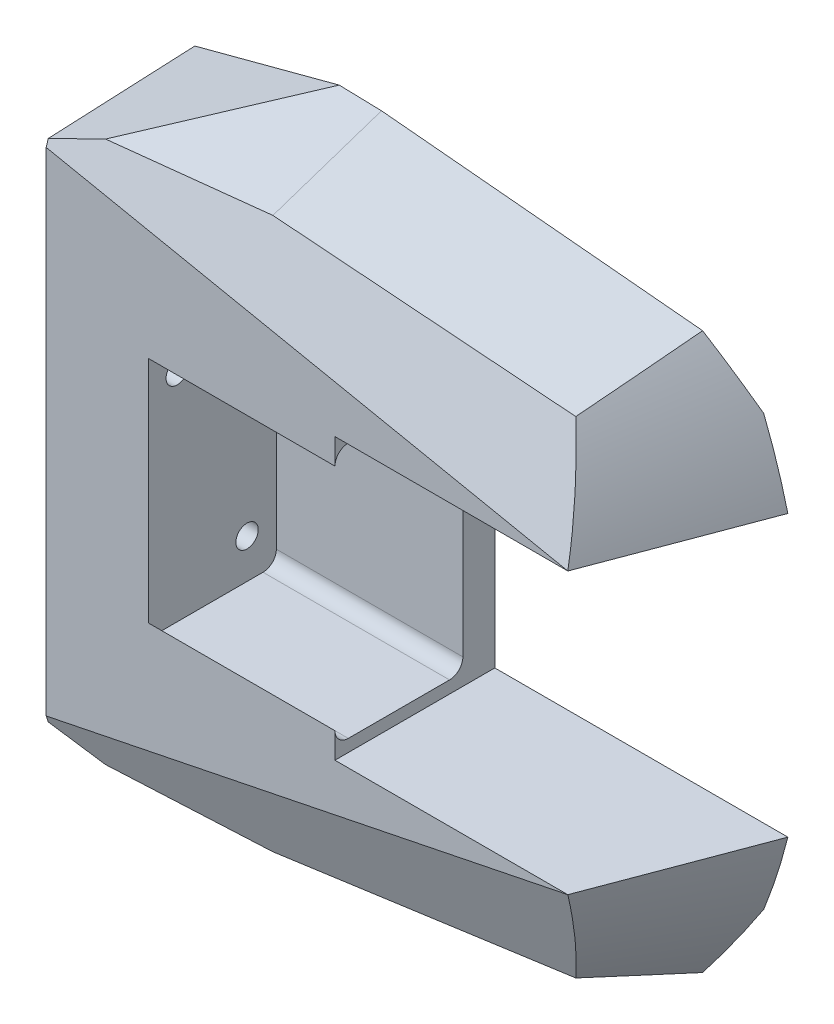
SolidWorks part; units mm, degrees
material "7075-O (SS)"
ref_plane "Top Plane" through (0, 0, 0) normal (0, 0, 1) x (1, 0, 0)
ref_plane "Front Plane" through (0, 0, 0) normal (0, 1, 0) x (1, 0, 0)
ref_plane "Right Plane" through (0, 0, 0) normal (1, 0, 0) x (0, 0, -1)
sketch "Sketch2" plane through (0, 0, 0) normal (0, 0, 1) x (1, 0, 0)
  line L0 (-50, 46.6303) -> (-41.2217, 50)
  line L1 (50, -50) -> (-50, -50)
  line L2 (50, -50) -> (50, 50)
  line L3 (50, 50) -> (-50, 50)
  line L4 (-50, -50) -> (-50, 50)
  line L5 (50, -50) -> (-50, 50) construction
  line L6 (50, 50) -> (-50, -50) construction
  line L7 (-10.1637, 50) -> (50, 42.6128)
  line L8 (-50, 0) -> (50, 0) construction
  line L9 (-10.1637, -50) -> (50, -42.6128)
  line L10 (-50, -46.6303) -> (-41.2217, -50)
  line L11 (50, 26.3007) -> (26.3007, 26.3007)
  line L12 (50, -26.3007) -> (26.3007, -26.3007)
  line L13 (26.3007, -26.3007) -> (26.3007, 26.3007)
  arc A0 (43.4207, 43.4207) -> (43.4207, -43.4207) centre (-44, 0) cw
  point P0 (0, 0)
  point P19 (50, -26.3007)
  point P20 (50, 26.3007)
  dimension "D1" = 100
  dimension "D2" = 100
  dimension "D3" = 69
  dimension "D4" = 3.3697
  dimension "D5" = 83
  dimension "D6" = 7.3872
  dimension "D7" = 44
extrude "Boss-Extrude1" add sketch "Sketch2" along normal blind 30 contours A0 L12 L13 L11 L7 L3 L0 L4 L10 L1 L9
sketch "Sketch3" plane through (26.3007, 0, 0) normal (1, 0, 0) x (0, 0, -1)
  line L0 (-30, 26.3007) -> (0, 26.3007) construction
  line L1 (-30, -26.3007) -> (0, -26.3007)
  line L2 (-30, -26.3007) -> (-30, 26.3007)
  line L3 (-30, 26.3007) -> (0, 26.3007)
  line L4 (0, -26.3007) -> (0, 26.3007)
extrude "Cut-Extrude1" cut sketch "Sketch3" against normal blind 20
draft "Draft1" type of draft neutral plane draft angle 20 faces to draft 6 face at (-25.6927, 50, 15) face at (16.6285, 46.7103, 15) face at (46.9118, 34.9381, 15) face at (46.9118, -34.9381, 15) face at (-25.6927, -50, 15) face at (16.6285, -46.7103, 15) neutral plane through (0, 0, 30) neutral plane normal (0, 0, 1) parameters "D1"=20
sketch "Sketch5" plane through (-50, 0, 0) normal (-1, 0, 0) x (0, 0, 1)
  line L0 (0, -46.6303) -> (0, 46.6303) construction
  line L9 (0, 42) -> (23, 42)
  line L10 (0, 42) -> (0, -42)
  line L11 (0, -42) -> (23, -42)
  line L12 (28, 37) -> (28, -37)
  arc A0 (28, -37) -> (23, -42) centre (23, -37) cw
  arc A1 (28, 37) -> (23, 42) centre (23, 37) ccw
  point P15 (28, -42)
  point P18 (28, 42)
  dimension "D4" = 5
  dimension "D1" = 42
  dimension "D2" = 84
  dimension "D3" = 28
extrude "Cut-Extrude2" cut sketch "Sketch5" against normal blind 5
sketch "Sketch6" plane through (0, 0, 0) normal (0, 0, -1) x (-1, 0, 0)
  line L1 (45, 42) -> (10, 42)
  line L2 (45, 42) -> (45, -42)
  line L3 (45, -42) -> (10, -42)
  line L4 (5, 37) -> (5, -37)
  arc A0 (10, -42) -> (5, -37) centre (10, -37) cw
  arc A1 (10, 42) -> (5, 37) centre (10, 37) ccw
  point P7 (5, -42)
  point P10 (5, 42)
  dimension "D3" = 5
  dimension "D1" = 40
  dimension "D2" = 84
extrude "Cut-Extrude3" cut sketch "Sketch6" against normal blind 5
sketch "Sketch7" plane through (0, 0, 5) normal (0, 0, -1) x (-1, 0, 0)
  point P0 (29.9, 29.8957)
  point P3 (29.9, -29.8957)
hole_wizard "M6x1.0 Tapped Hole1" positions "Sketch7" profile "Sketch8" tap size "M6x1.0" standard "ANSI Metric"
sketch "Sketch8" plane through (-29.9, 29.8957, 5) normal (1, 0, 0) x (0, 1, 0)
  line L0 (0, 0) -> (0, 11.5022)
  line L1 (0, 11.5022) -> (2.5, 10)
  line L2 (2.5, 10) -> (2.5, 0)
  line L5 (2.5, 0) -> (0, 0)
  line L10 (0, 11.5022) -> (-2.5, 10) construction
  line L11 (0, -6.35) -> (0, 107.95) construction
  dimension "Tap Drill Dia." = 5
  dimension "Tap Drill Depth" = 10
  dimension "Drill Angle" = 118
cosmetic thread "Hole Thread1" parameters "D1"=12, "D2"=6
cosmetic thread "Hole Thread2" parameters "D1"=12, "D2"=6
sketch "Sketch9" plane through (0, 0, 0) normal (0, 0, -1) x (-1, 0, 0)
  line L0 (50, 46.6303) -> (-56.7679, 40.304)
  line L4 (50, 46.6303) -> (18.1671, 64.9129)
  line L5 (18.1671, 64.9129) -> (-51.4723, 56.583)
  arc A0 (-50.3888, 53.5662) -> (-61.2941, 26.3007) centre (44, 0) ccw construction
  arc A3 (-56.7679, 40.304) -> (-51.4723, 56.583) centre (56.438, 12.4787) cw
revolve "Cut-Revolve1" cut sketch "Sketch9" angle 20 about L0
sketch "Sketch11" plane through (0, 0, 0) normal (0, 0, -1) x (-1, 0, 0)
  line L0 (50, -46.6303) -> (-56.7679, -40.304)
  line L1 (50, -46.6303) -> (21.2236, -65.429)
  line L2 (21.2236, -65.429) -> (-53.454, -56.7727)
  arc A0 (-61.2941, -26.3007) -> (-50.3888, -53.5662) centre (44, 0) ccw construction
  arc A1 (-53.454, -56.7727) -> (-56.7679, -40.304) centre (59.1366, -25.5487) cw
revolve "Cut-Revolve2" cut sketch "Sketch11" angle 20 about L0
sketch "Sketch13" plane through (0, 0, 30) normal (0, 0, 1) x (1, 0, 0)
  line L0 (-50, 46.6303) -> (50, 26.3007)
  line L1 (50, 26.3007) -> (49.447, 52.16)
  line L2 (49.447, 52.16) -> (-50, 58.9949)
  line L3 (-50, 58.9949) -> (-50, 46.6303)
revolve "Cut-Revolve3" cut sketch "Sketch13" angle 20 about L0
sketch "Sketch14" plane through (0, 0, 30) normal (0, 0, 1) x (1, 0, 0)
  line L5 (50, -26.3007) -> (49.447, -52.16)
  line L6 (50, -26.3007) -> (-50, -46.6303)
  line L7 (-50, -46.6303) -> (-50, -58.9953)
  line L8 (-50, -58.9953) -> (49.447, -52.16)
  dimension "D1" = 12.365
revolve "Cut-Revolve4" cut sketch "Sketch14" angle 20 about L6
sketch "Sketch15" plane through (6.3007, 0, 0) normal (1, 0, 0) x (0, 0, -1)
  line L18 (-30, 0) -> (-30, -21.5)
  line L19 (-30, 26.3007) -> (-30, -26.3007) construction
  line L20 (-27.5, -24) -> (-8.5, -24)
  line L21 (-6, -21.5) -> (-6, 21.5)
  line L22 (-8.5, 24) -> (-27.5, 24)
  line L23 (-30, 21.5) -> (-30, 0)
  arc A0 (-8.5, -24) -> (-6, -21.5) centre (-8.5, -21.5) ccw
  arc A1 (-6, 21.5) -> (-8.5, 24) centre (-8.5, 21.5) ccw
  arc A2 (-27.5, 24) -> (-30, 21.5) centre (-27.5, 21.5) ccw
  arc A3 (-30, -21.5) -> (-27.5, -24) centre (-27.5, -21.5) ccw
  point P9 (-6, -24)
  point P14 (-30, 24)
  point P17 (-30, -24)
  dimension "D4" = 2.5
  dimension "D1" = 24
  dimension "D2" = 24
  dimension "D3" = 24
extrude "Cut-Extrude4" cut sketch "Sketch15" against normal blind 35
sketch "Sketch16" plane through (-28.6993, 0, 0) normal (1, 0, 0) x (0, 0, -1)
  point P0 (-11.498, -16.6054)
  point P3 (-24.602, 16.6054)
hole_wizard "M5x0.8 Tapped Hole1" positions "Sketch16" profile "Sketch17" tap size "M5x0.8" standard "ANSI Metric" end condition through all
sketch "Sketch17" plane through (-28.6993, -16.6054, 11.498) normal (0, 1, 0) x (0, 0, -1)
  line L0 (0, 0) -> (0, 21.3007)
  line L1 (0, 21.3007) -> (2.1, 21.3007)
  line L2 (2.1, 21.3007) -> (2.1, 0)
  line L5 (2.1, 0) -> (0, 0)
  line L11 (0, -6.35) -> (0, 107.95) construction
  dimension "Thru Tap Drill Dia." = 4.2
  dimension "Thru Tap Drill Depth" = 21.3007
cosmetic thread "Hole Thread3" parameters "D2"=5
cosmetic thread "Hole Thread4" parameters "D2"=5
sketch "Sketch19" plane through (-50, 0, 0) normal (-1, 0, 0) x (0, 0, 1)
  line L1 (0, 58.8905) -> (47.5161, 58.8905)
  line L2 (0, 58.8905) -> (0, -58.8905)
  line L3 (0, -58.8905) -> (47.5161, -58.8905)
  line L4 (47.5161, 58.8905) -> (47.5161, -58.8905)
revolve "Cut-Revolve5" cut sketch "Sketch19" angle 4 about L2
sketch "Sketch20" plane through (0, 0, 0) normal (0, 0, -1) x (-1, 0, 0)
  arc A0 (-56.7679, 40.304) -> (-61.2941, 26.3007) centre (44, 0) ccw construction
  arc A1 (-61.2941, -26.3007) -> (-56.7679, -40.304) centre (44, 0) ccw construction
  point P0 (-50.2687, 33.3791)
  point P2 (-50.2687, -33.3791)
  point P4 (-36.2687, -33.3791)
  point P6 (-22.2687, -33.3791)
  point P8 (-36.2687, 33.3791)
  point P10 (-22.2687, 33.3791)
  point P16 (-59.2687, 33.3791)
  point P20 (-59.2687, -33.3791)
  dimension "D1" = 9
  dimension "D2" = 14
  dimension "D3" = 14
  dimension "D4" = 9
  dimension "D5" = 14
  dimension "D6" = 14
  dimension "D7" = 66.7583
hole_wizard "M5x0.8 Tapped Hole2" positions "Sketch20" profile "Sketch21" tap size "M5x0.8" standard "ANSI Metric"
sketch "Sketch21" plane through (50.2687, 33.3791, 0) normal (1, 0, 0) x (0, 1, 0)
  line L0 (0, 0) -> (0, 11.2618)
  line L1 (0, 11.2618) -> (2.1, 10)
  line L2 (2.1, 10) -> (2.1, 3.15)
  line L3 (2.1, 3.15) -> (5.25, 0)
  line L5 (5.25, 0) -> (0, 0)
  line L6 (-2.1, 3.15) -> (-5.25, 0) construction
  line L10 (0, 11.2618) -> (-2.1, 10) construction
  line L11 (0, -6.35) -> (0, 107.95) construction
  dimension "Tap Drill Dia." = 4.2
  dimension "Tap Drill Depth" = 10
  dimension "Near C'Sink Dia." = 10.5
  dimension "Near C'Sink Angle" = 90
  dimension "Drill Angle" = 118
cosmetic thread "Hole Thread5" parameters "D1"=10, "D2"=5
cosmetic thread "Hole Thread6" parameters "D1"=10, "D2"=5
cosmetic thread "Hole Thread7" parameters "D1"=10, "D2"=5
cosmetic thread "Hole Thread8" parameters "D1"=10, "D2"=5
cosmetic thread "Hole Thread9" parameters "D1"=10, "D2"=5
cosmetic thread "Hole Thread10" parameters "D1"=10, "D2"=5
